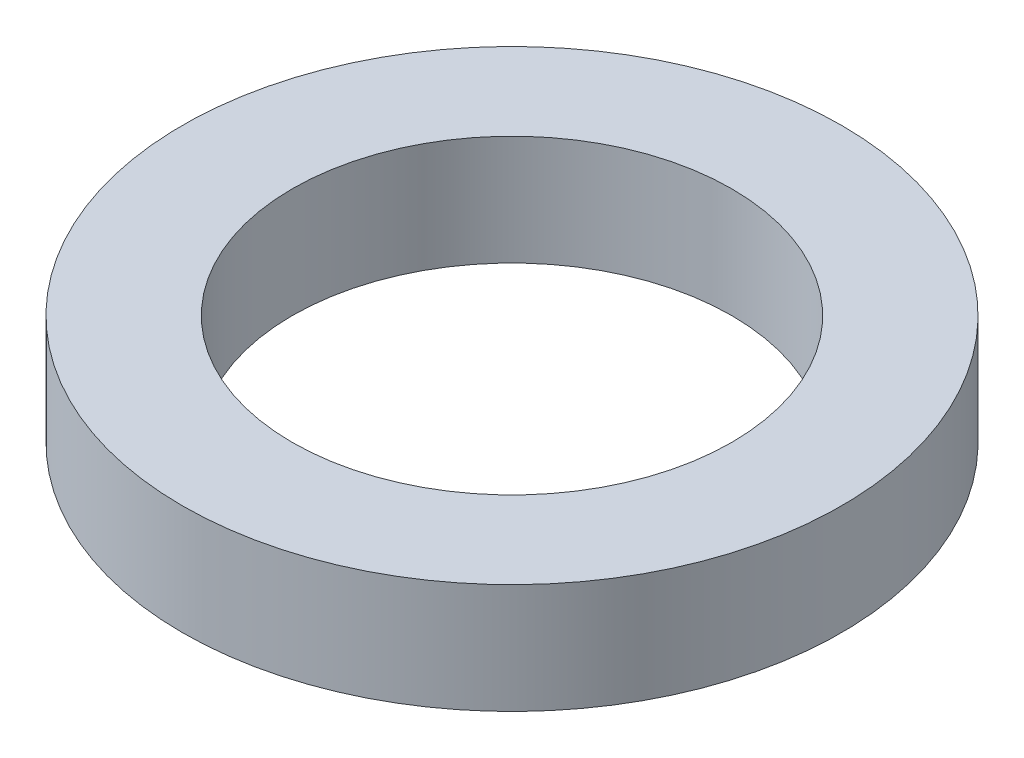
SolidWorks part; units mm, degrees
material "Brass"
ref_plane "Front Plane" through (0, 0, 0) normal (0, 0, 1) x (1, 0, 0)
ref_plane "Top Plane" through (0, 0, 0) normal (0, 1, 0) x (1, 0, 0)
ref_plane "Right Plane" through (0, 0, 0) normal (1, 0, 0) x (0, 0, -1)
sketch "Sketch1" plane through (0, 0, 0) normal (0, 1, 0) x (1, 0, 0)
  circle A0 centre (0, 0) radius 1.5
  circle A1 centre (0, 0) radius 1
  dimension "D1" = 0.5
  dimension "D2" = 2
extrude "Boss-Extrude1" add sketch "Sketch1" along normal blind 0.5
